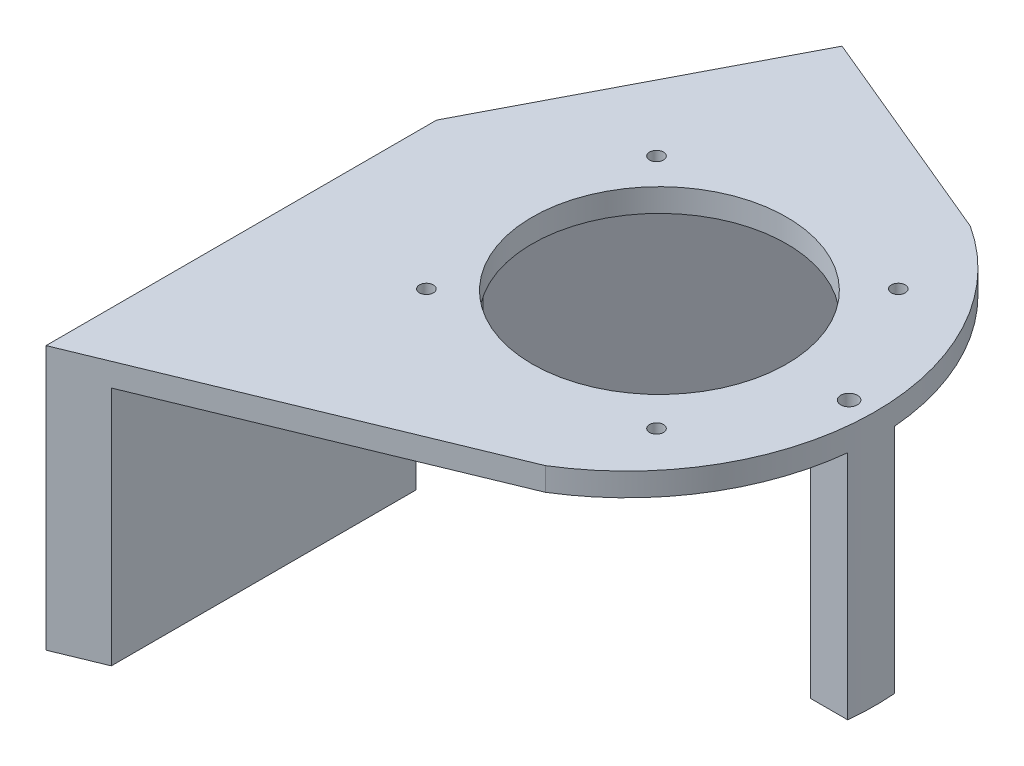
SolidWorks part; units mm, degrees
ref_plane "Front Plane" through (0, 0, 0) normal (0, 0, 1) x (1, 0, 0)
ref_plane "Top Plane" through (0, 0, 0) normal (0, 1, 0) x (1, 0, 0)
ref_plane "Right Plane" through (0, 0, 0) normal (1, 0, 0) x (0, 0, -1)
sketch "Sketch2" plane through (0, 0, 0) normal (0, 1, 0) x (1, 0, 0)
  line L10 (109.5019, -38.9151) -> (155.4788, -38.9151) construction
  line L16 (104.5, -77.2) -> (142.7026, -61.4563)
  line L23 (109.5, -35) -> (123.6013, -7.8719) construction
  line L26 (104.5, 0) -> (104.5, -77.2) construction
  line L27 (109.5, -35) -> (104.5, -35) construction
  line L29 (104.5, -42.2) -> (109.5, -42.2) construction
  line L30 (109.5, -42.2) -> (109.5, -75.1394) construction
  line L31 (116.4903, -54.6) -> (148.4903, -22.6) construction
  line L36 (116.4903, -22.6) -> (148.4903, -54.6) construction
  line L37 (104.5, -35) -> (119.4834, -6.1748) construction
  line L38 (104.5, -35) -> (119.4834, -6.1748)
  line L39 (143.2356, -16.0801) -> (119.4834, -6.1748)
  line L40 (104.5, -35) -> (104.5, -77.2)
  line L41 (155.4788, -31.0466) -> (155.4788, -48.7495) construction
  line L42 (153.0855, -35.9151) -> (158.1488, -35.9151) construction
  line L43 (153.0855, -41.9151) -> (158.1488, -41.9151) construction
  arc A2 (143.2356, -16.0801) -> (142.7026, -61.4563) centre (128.65, -38.6) cw
  circle A3 centre (132.4903, -38.9151) radius 13.75
  circle A4 centre (145.2365, -25.8538) radius 0.75
  circle A5 centre (119.7442, -51.3462) radius 0.75
  circle A6 centre (119.7442, -26.4841) radius 0.75
  circle A7 centre (145.2365, -51.9765) radius 0.75
  dimension "D3" = 35
  dimension "D5" = 32
  dimension "D9" = 18.25
  dimension "D7" = 3
  dimension "D8" = 3
  dimension "D1" = 35
  dimension "D2" = 5
  dimension "D4" = 5
  dimension "D6" = 32
extrude "Boss-Extrude1" add sketch "Sketch2" along normal blind 2.5
sketch "Sketch3" plane through (0, 0, 0) normal (0, -1, 0) x (1, 0, 0)
  line L11 (104.5, 42.2) -> (109.5, 42.2)
  line L12 (109.5, 42.2) -> (109.5, 75.1394)
  line L13 (109.5, 75.1394) -> (104.5, 77.2)
  line L14 (104.5, 77.2) -> (104.5, 42.2)
  line L15 (109.5, 35) -> (104.5, 35)
  line L16 (104.5, 35) -> (119.4834, 6.1748)
  line L17 (119.4834, 6.1748) -> (123.6013, 7.8719)
  line L18 (123.6013, 7.8719) -> (109.5, 35)
extrude "Boss-Extrude2" add sketch "Sketch3" along normal blind 26
sketch "Sketch5" plane through (104.5, 0, 0) normal (-1, 0, 0) x (0, 0, 1)
  line L0 (42.2, -26) -> (42.2, 0) construction
  line L1 (35, 0) -> (42.2, 0)
  line L2 (35, 0) -> (35, -21)
  line L3 (35, -21) -> (42.2, -21)
  line L4 (42.2, 0) -> (42.2, -21)
  line L5 (77.2, -26) -> (42.2, -26) construction
  dimension "D1" = 5
extrude "Boss-Extrude5" add sketch "Sketch5" against normal blind 5
sketch "Sketch6" plane through (0, 0, 0) normal (0, -1, 0) x (1, 0, 0)
  line L0 (155.3326, 41.4151) -> (151.3326, 41.4151)
  line L1 (151.3326, 41.4151) -> (151.3326, 36.4151)
  line L2 (151.3326, 36.4151) -> (155.3915, 36.4151)
  line L3 (109.5019, 38.9151) -> (155.4788, 38.9151) construction
  line L4 (152.9788, 40.3047) -> (152.9788, 37.683) construction
  arc A0 (155.3326, 41.4151) -> (155.3915, 36.4151) centre (128.65, 38.6) cw
  arc A1 (143.2356, 16.0801) -> (142.7026, 61.4563) centre (128.65, 38.6) ccw construction
  circle A2 centre (152.9788, 38.9151) radius 0.9
  dimension "D1" = 2.5
  dimension "D2" = 2.5
  dimension "D3" = 4
  dimension "D4" = 2.5
extrude "Boss-Extrude6" add sketch "Sketch6" along normal blind 25 contours A0 L2 L1 L0
sketch "Sketch7" plane through (0, 2.5, 0) normal (0, 1, 0) x (1, 0, 0)
  circle A0 centre (152.9788, -38.9151) radius 0.9
extrude "Cut-Extrude1" cut sketch "Sketch7" against normal blind 10
